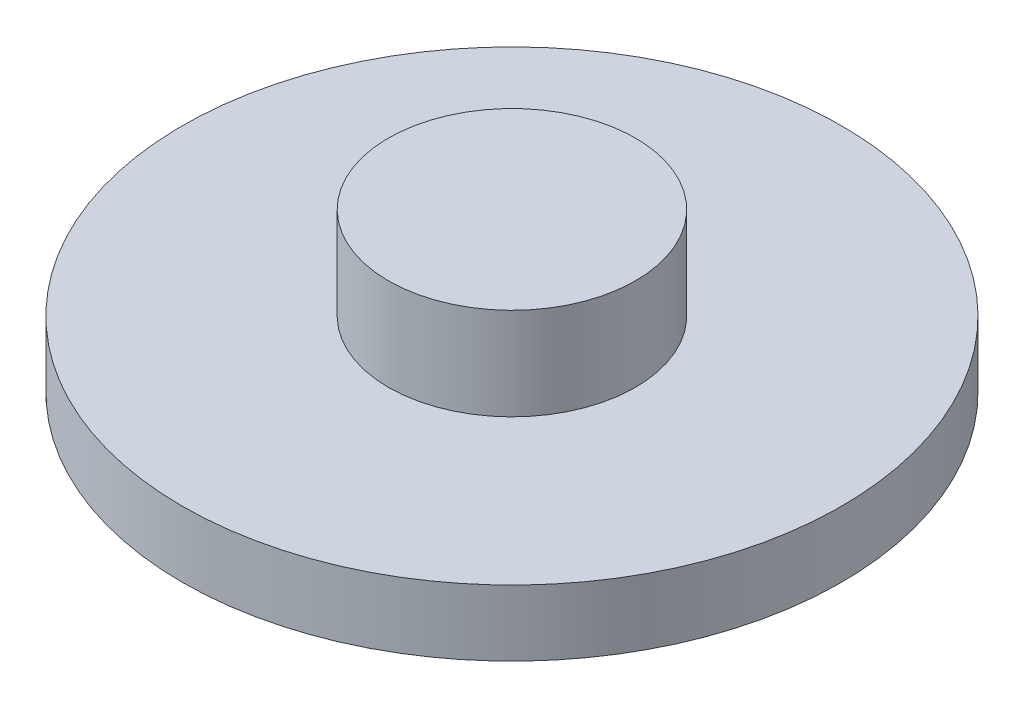
SolidWorks part; units mm, degrees
ref_plane "Front Plane" through (0, 0, 0) normal (0, 0, 1) x (1, 0, 0)
ref_plane "Top Plane" through (0, 0, 0) normal (0, 1, 0) x (1, 0, 0)
ref_plane "Right Plane" through (0, 0, 0) normal (1, 0, 0) x (0, 0, -1)
sketch "Sketch1" plane through (0, 0, 0) normal (0, 1, 0) x (1, 0, 0)
  circle A0 centre (0, 0) radius 25.4
  dimension "D1" = 50.8
extrude "Boss-Extrude1" add sketch "Sketch1" along normal blind 5.08
sketch "Sketch4" plane through (0, 5.08, 0) normal (0, 1, 0) x (1, 0, 0)
  circle A0 centre (0, 0) radius 9.525
  dimension "D1" = 19.05
extrude "Boss-Extrude2" add sketch "Sketch4" along normal blind 7.112
